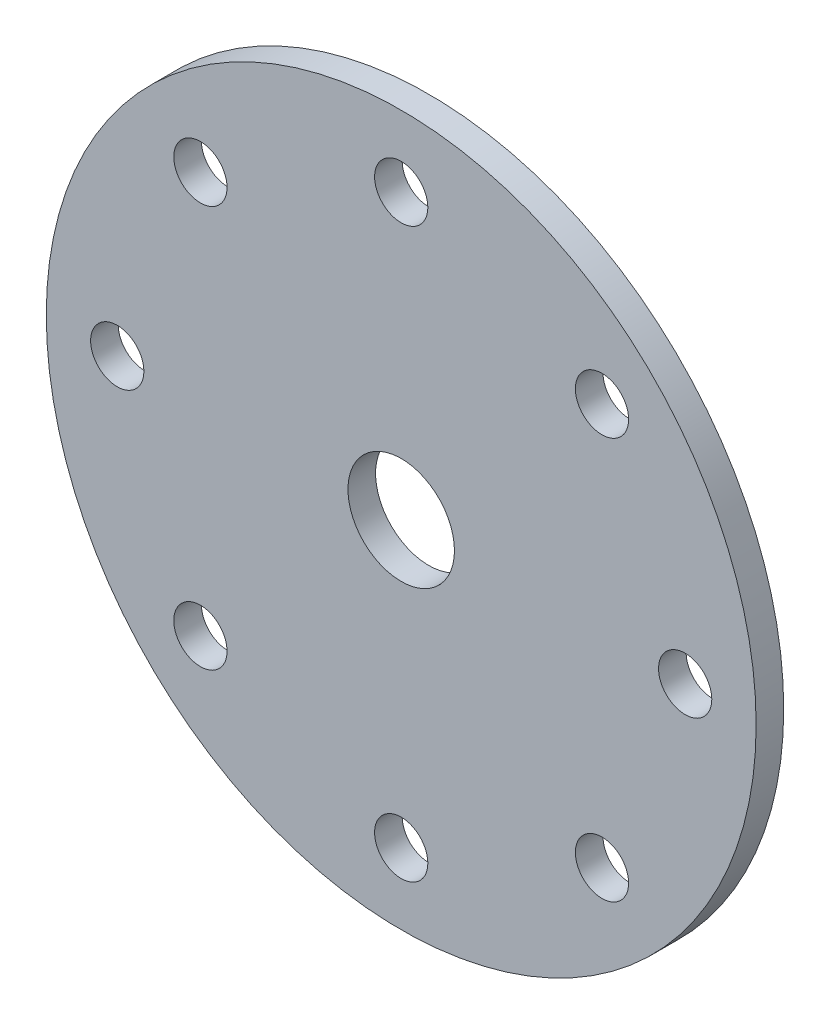
SolidWorks part; units mm, degrees
material "Plain Carbon Steel"
ref_plane "Front Plane" through (0, 0, 0) normal (0, 0, 1) x (1, 0, 0)
ref_plane "Top Plane" through (0, 0, 0) normal (0, 1, 0) x (1, 0, 0)
ref_plane "Right Plane" through (0, 0, 0) normal (1, 0, 0) x (0, 0, -1)
sketch "Sketch1" plane through (0, 0, 0) normal (0, 0, 1) x (1, 0, 0)
  line L0 (0, 63.5) -> (0, -63.5) construction
  line L1 (-63.5, 0) -> (63.5, 0) construction
  line L2 (-35.921, 35.921) -> (35.921, -35.921) construction
  line L3 (-35.921, -35.921) -> (35.921, 35.921) construction
  circle A0 centre (0, 0) radius 63.5
  circle A1 centre (0, 0) radius 9.525
  circle A2 centre (0, 50.8) radius 4.7625
  circle A6 centre (35.921, 35.921) radius 4.7625
  circle A7 centre (50.8, 0) radius 4.7625
  circle A8 centre (35.921, -35.921) radius 4.7625
  circle A9 centre (0, -50.8) radius 4.7625
  circle A10 centre (-35.921, -35.921) radius 4.7625
  circle A11 centre (-50.8, 0) radius 4.7625
  circle A12 centre (-35.921, 35.921) radius 4.7625
  dimension "D1" = 127
  dimension "D2" = 19.05
  dimension "D3" = 9.525
  dimension "D6" = 12.7
  dimension "D4" = 12.7
  dimension "D5" = 8
extrude "Rotor Disc" add sketch "Sketch1" along normal blind 4.9352
